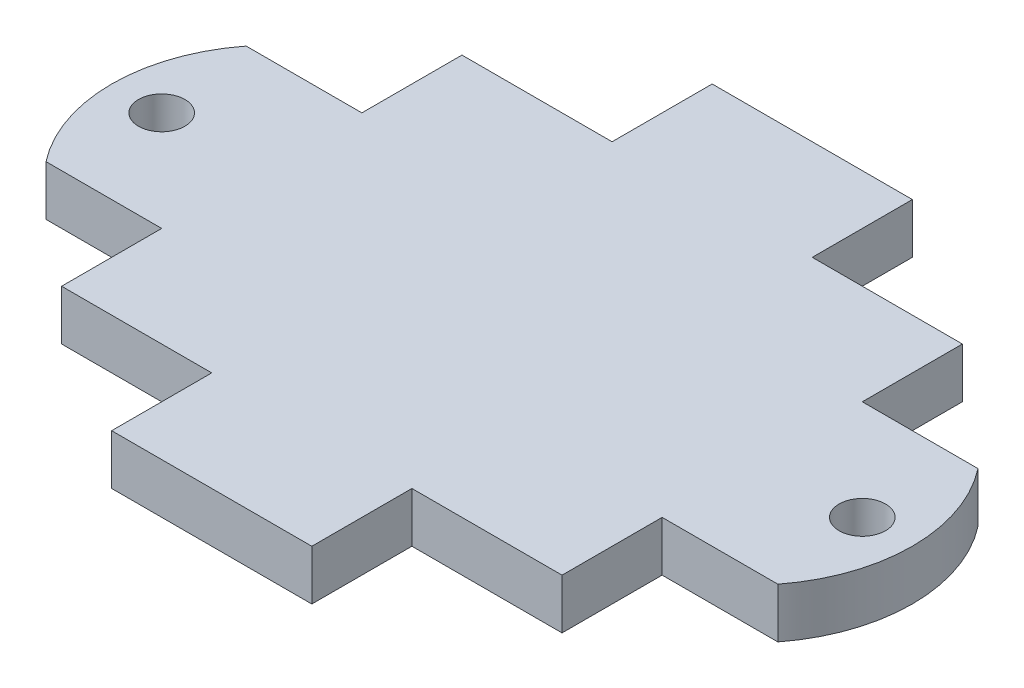
SolidWorks part; units mm, degrees
material "Acrylic (Medium-high impact)"
ref_plane "Front Plane" through (0, 0, 0) normal (0, 0, 1) x (1, 0, 0)
ref_plane "Top Plane" through (0, 0, 0) normal (0, 1, 0) x (1, 0, 0)
ref_plane "Right Plane" through (0, 0, 0) normal (1, 0, 0) x (0, 0, -1)
sketch "Sketch1" plane through (0, 0, 0) normal (0, 1, 0) x (1, 0, 0)
  line L0 (0, 2.5414) -> (0, -2.9418) construction
  line L1 (-15.875, 12.7) -> (-6.35, 12.7)
  line L2 (-15.875, 12.7) -> (-15.875, 6.35)
  line L3 (-15.875, -12.7) -> (-6.35, -12.7)
  line L4 (15.875, 12.7) -> (15.875, 6.35)
  line L5 (-15.875, 12.7) -> (15.875, -12.7) construction
  line L6 (-15.875, -12.7) -> (15.875, 12.7) construction
  line L7 (-15.875, 6.35) -> (-19.05, 6.35)
  line L8 (-19.05, 6.35) -> (-19.05, -6.35) construction
  line L9 (-15.875, -6.35) -> (-19.05, -6.35)
  line L10 (15.875, -6.35) -> (19.05, -6.35)
  line L11 (15.875, 6.35) -> (19.05, 6.35)
  line L12 (-2.7203, 0) -> (5.2518, 0) construction
  line L13 (-15.875, -6.35) -> (-15.875, -12.7)
  line L15 (15.875, -6.35) -> (15.875, -12.7)
  line L16 (-6.35, 12.7) -> (-6.35, 19.05)
  line L17 (-6.35, 19.05) -> (6.35, 19.05)
  line L18 (6.35, 12.7) -> (6.35, 19.05)
  line L19 (6.35, -12.7) -> (6.35, -19.05)
  line L20 (-6.35, -19.05) -> (6.35, -19.05)
  line L21 (-6.35, -12.7) -> (-6.35, -19.05)
  line L22 (6.35, 12.7) -> (15.875, 12.7)
  line L23 (6.35, -12.7) -> (15.875, -12.7)
  line L27 (-19.05, 6.35) -> (-23.2148, 6.35)
  line L28 (-19.05, -6.35) -> (-23.2148, -6.35)
  line L29 (19.05, 6.35) -> (23.2148, 6.35)
  line L30 (19.05, -6.35) -> (23.2148, -6.35)
  arc A0 (-19.05, 6.35) -> (-19.05, -6.35) centre (-19.05, 0) ccw construction
  circle A1 centre (-22.225, 0) radius 3.175 construction
  arc A2 (19.05, 6.35) -> (19.05, -6.35) centre (19.05, 0) cw construction
  arc A3 (-23.2148, 6.35) -> (-23.2148, -6.35) centre (-15.0812, 0) ccw
  arc A4 (23.2148, 6.35) -> (23.2148, -6.35) centre (15.0812, 0) cw
  point P0 (0, 0)
  point P24 (0, 19.05)
  dimension "D3" = 6.35
  dimension "D8" = 10.3188
  dimension "D1" = 25.4
  dimension "D2" = 31.75
  dimension "D4" = 3.175
  dimension "D5" = 12.7
  dimension "D6" = 12.7
  dimension "D7" = 6.35
extrude "Boss-Extrude1" add sketch "Sketch1" along normal blind 3.175
hole_wizard "#4 Clearance Hole1" positions "Sketch3" profile "Sketch2" hole size "#4" standard "Ansi Inch"
sketch "Sketch3" plane through (0, 3.175, 0) normal (0, 1, 0) x (-1, 0, 0)
  line L2 (22.225, 0) -> (-22.225, 0) construction
  circle A3 centre (22.225, 0) radius 3.175 construction
  point P0 (-22.225, 0)
  point P1 (22.225, 0)
sketch "Sketch2" plane through (22.225, 3.175, 0) normal (1, 0, 0) x (0, 0, 1)
  line L0 (0, 0) -> (0, 7.2352)
  line L1 (0, 7.2352) -> (1.4732, 6.35)
  line L2 (1.4732, 6.35) -> (1.4732, 0)
  line L5 (1.4732, 0) -> (0, 0)
  line L10 (0, 7.2352) -> (-1.4732, 6.35) construction
  line L11 (0, -6.35) -> (0, 107.95) construction
  dimension "Hole Dia." = 2.9464
  dimension "Hole Depth" = 6.35
  dimension "Drill Angle" = 118
sketch "Sketch4" [suppressed] plane through (0, 3.175, 0) normal (0, 1, 0) x (1, 0, 0)
  point P0 (-19.05, 6.35)
  point P1 (-15.875, 6.35)
  point P3 (-6.35, 12.7)
  point P5 (6.35, 12.7)
  point P7 (15.875, 6.35)
  point P9 (19.05, 6.35)
  point P11 (15.875, -6.35)
  point P13 (19.05, -6.35)
  point P15 (6.35, -12.7)
  point P17 (-6.35, -12.7)
  point P19 (-15.875, -6.35)
  point P21 (-19.05, -6.35)
sketch "Sketch5" [suppressed] plane through (0, 3.175, 0) normal (0, 1, 0) x (1, 0, 0)
  circle A0 centre (-19.05, 6.35) radius 0.635
  dimension "D1" = 1.27
extrude "Cut-Extrude1" [suppressed] cut sketch "Sketch5" along normal blind 2.54 and the other way up to next
pattern_sketch "Sketch-Pattern1" [suppressed]
